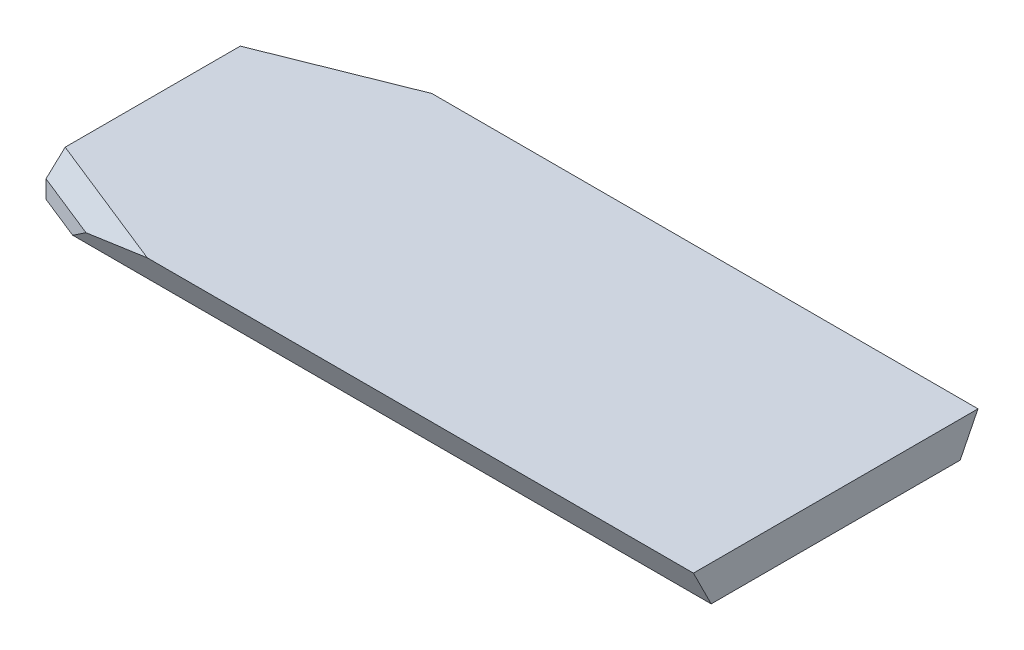
SolidWorks part; units mm, degrees
material "Chrome Stainless Steel"
ref_plane "Front Plane" through (0, 0, 0) normal (0, 0, 1) x (1, 0, 0)
ref_plane "Top Plane" through (0, 0, 0) normal (0, 1, 0) x (1, 0, 0)
ref_plane "Right Plane" through (0, 0, 0) normal (1, 0, 0) x (0, 0, -1)
sketch "Sketch3" plane through (0, 0, 0) normal (1, 0, 0) x (0, 0, -1)
  line L0 (0, 0) -> (0, 6.4266) construction
  line L1 (-20, 5) -> (-17.5, 0)
  line L2 (-17.5, 0) -> (17.5, 0)
  line L3 (20, 5) -> (-20, 5)
  line L4 (20, 5) -> (17.5, 0)
  dimension "D1" = 17.5
  dimension "D2" = 40
  dimension "D3" = 35
  dimension "D4" = 5
extrude "Boss-Extrude2" add sketch "Sketch3" along normal blind 96
sketch "Sketch5" plane through (0, 5, 0) normal (0, 1, 0) x (1, 0, 0)
  line L0 (12.5, 20) -> (12.5, -20) construction
  line L1 (96, 20) -> (0, 20) construction
  line L2 (96, -20) -> (0, -20) construction
  line L3 (0, 20) -> (0, -20) construction
  line L4 (0, 15) -> (17.6226, 15) construction
  line L5 (0, 15) -> (12.5, 20)
  line L6 (12.5, 20) -> (0, 20)
  line L7 (0, 20) -> (0, 15)
  line L9 (12.5, 0) -> (1.4673, 0) construction
  line L10 (0, -20) -> (0, -15)
  line L11 (0, -15) -> (12.5, -20)
  line L12 (12.5, -20) -> (0, -20)
  dimension "D1" = 12.5
  dimension "D2" = 5
extrude "Cut-Extrude1" cut sketch "Sketch5" against normal up to next
chamfer "Chamfer1" distance 2.5 angle 45 2 edges at (6.25, 5, 17.5) (6.25, 5, -17.5)
sketch "Sketch6" plane through (0, 0, 0) normal (0, -1, 0) x (1, 0, 0)
  line L0 (30, 50.6175) -> (30, -47.29) construction
  line L1 (0, 15) -> (0, -15) construction
  line L2 (-1.7085, -42) -> (34.6063, -42) construction
  line L4 (96, -20) -> (19.2315, -20) construction
  circle A0 centre (30, -42) radius 12.5 construction
  dimension "D3" = 25
  dimension "D1" = 30
  dimension "D2" = 22
hole_wizard "Ø4.0mm Dowel Hole1" positions "Sketch7" profile "Sketch8" hole size "Ø4.0" standard "ANSI Metric"
sketch "Sketch7" plane through (0, 0, 0) normal (0, -1, 0) x (-1, 0, 0)
  line L0 (0, -15) -> (0, 15) construction
  line L1 (-96, -17.5) -> (-6.25, -17.5) construction
  line L2 (-96, 17.5) -> (-6.25, 17.5) construction
  point P0 (-23, 9)
  point P2 (-80, -9)
  dimension "D1" = 23
  dimension "D2" = 80
  dimension "D3" = 26.5
  dimension "D4" = 26.5
sketch "Sketch8" plane through (23, 0, -9) normal (1, 0, 0) x (0, 0, -1)
  line L0 (0, 0) -> (0, 4)
  line L1 (0, 4) -> (2, 4)
  line L2 (2, 4) -> (2, 0)
  line L5 (2, 0) -> (0, 0)
  line L10 (0, 4) -> (-2, 4) construction
  line L11 (0, -6.35) -> (0, 107.95) construction
  dimension "Hole Dia." = 4
  dimension "Hole Depth" = 4
  dimension "Drill Angle" = 180
hole_wizard "M4x0.7 Tapped Hole1" positions "Sketch9" profile "Sketch10" tap size "M4x0.7" standard "ANSI Metric"
sketch "Sketch9" plane through (0, 0, 0) normal (0, -1, 0) x (-1, 0, 0)
  line L0 (0, -15) -> (0, 15) construction
  line L3 (-96, 17.5) -> (-6.25, 17.5) construction
  line L4 (-96, -17.5) -> (-6.25, -17.5) construction
  point P0 (-23, -9)
  point P2 (-80, 9)
  dimension "D1" = 23
  dimension "D2" = 80
  dimension "D3" = 26.5
  dimension "D4" = 26.5
sketch "Sketch10" plane through (23, 0, 9) normal (1, 0, 0) x (0, 0, -1)
  line L0 (0, 0) -> (0, 4.9914)
  line L1 (0, 4.9914) -> (1.65, 4)
  line L2 (1.65, 4) -> (1.65, 0)
  line L5 (1.65, 0) -> (0, 0)
  line L10 (0, 4.9914) -> (-1.65, 4) construction
  line L11 (0, -6.35) -> (0, 107.95) construction
  dimension "Tap Drill Dia." = 3.3
  dimension "Tap Drill Depth" = 4
  dimension "Drill Angle" = 118
cosmetic thread "Hole Thread1" parameters "D1"=4.5, "D2"=4
cosmetic thread "Hole Thread2" parameters "D1"=4.5, "D2"=4
